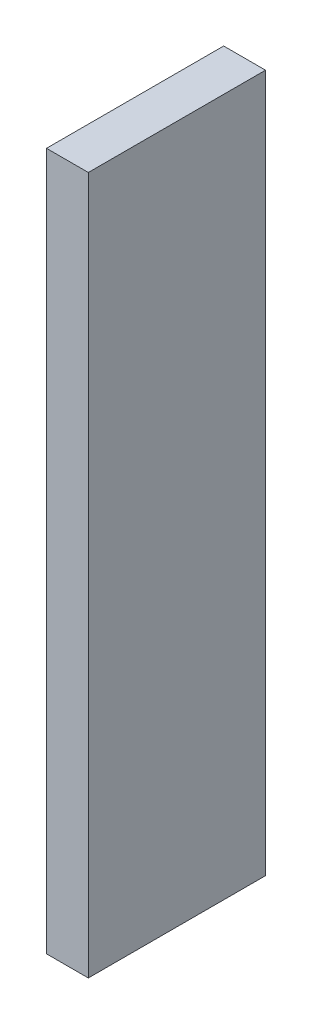
SolidWorks part; units mm, degrees
ref_plane "Front Plane" through (0, 0, 0) normal (0, 0, 1) x (1, 0, 0)
ref_plane "Top Plane" through (0, 0, 0) normal (0, 1, 0) x (1, 0, 0)
ref_plane "Right Plane" through (0, 0, 0) normal (1, 0, 0) x (0, 0, -1)
sketch "Sketch1" plane through (0, 0, 0) normal (0, 1, 0) x (1, 0, 0)
  line L1 (0.75, -3.175) -> (-0.75, -3.175)
  line L2 (0.75, -3.175) -> (0.75, 3.175)
  line L3 (0.75, 3.175) -> (-0.75, 3.175)
  line L4 (-0.75, -3.175) -> (-0.75, 3.175)
  line L5 (0.75, -3.175) -> (-0.75, 3.175) construction
  line L6 (0.75, 3.175) -> (-0.75, -3.175) construction
  point P0 (0, 0)
  dimension "D1" = 1.5
  dimension "D2" = 6.35
extrude "Boss-Extrude1" add sketch "Sketch1" along normal blind 25
